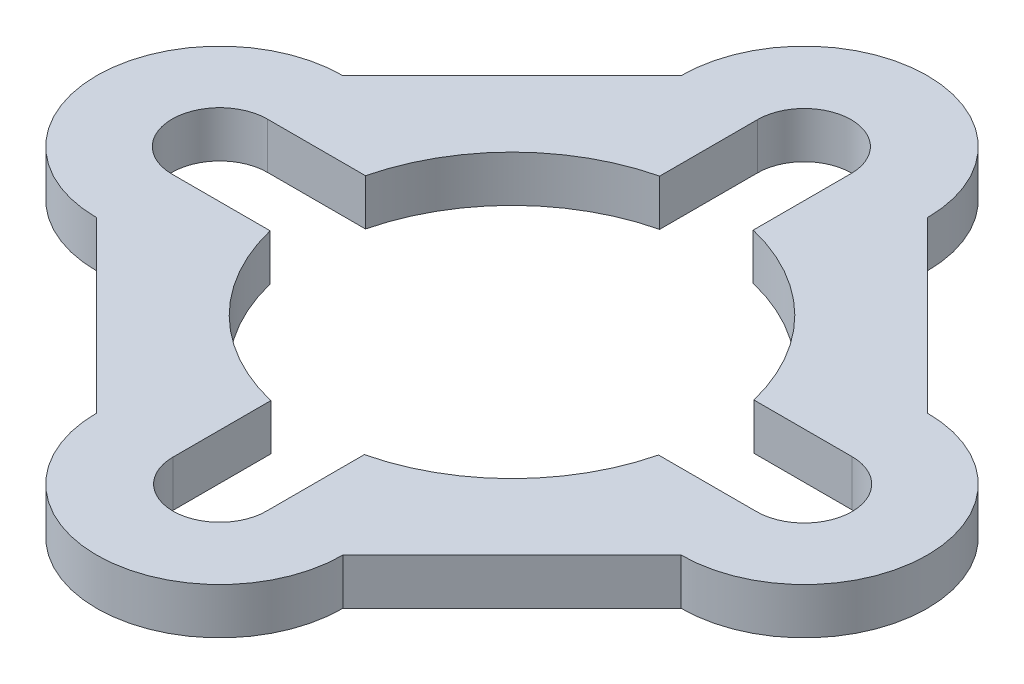
SolidWorks part; units mm, degrees
ref_plane "Front Plane" through (0, 0, 0) normal (0, 0, 1) x (1, 0, 0)
ref_plane "Top Plane" through (0, 0, 0) normal (0, 1, 0) x (1, 0, 0)
ref_plane "Right Plane" through (0, 0, 0) normal (1, 0, 0) x (0, 0, -1)
sketch "Sketch10" plane through (0, 0, 0) normal (0, 1, 0) x (1, 0, 0)
  line L0 (-9.5, 0) -> (9.5, 0) construction
  line L1 (-9.5, 1.55) -> (9.5, 1.55)
  line L2 (-9.5, -1.55) -> (9.5, -1.55)
  line L3 (0, 9.5) -> (0, -9.5) construction
  line L4 (1.52, 9.5) -> (1.52, -9.5)
  line L5 (-1.52, 9.5) -> (-1.52, -9.5)
  line L6 (-9.5, -4) -> (-4, -9.5)
  line L7 (4, -9.5) -> (9.5, -4)
  line L8 (9.5, 4) -> (4, 9.5)
  line L9 (-4, 9.5) -> (-9.5, 4)
  circle A4 centre (0, 0) radius 14.6 construction
  circle A5 centre (0, 0) radius 6.5
  arc A6 (-9.5, 1.55) -> (-9.5, -1.55) centre (-9.5, 0) ccw
  arc A7 (9.5, -1.55) -> (9.5, 1.55) centre (9.5, 0) ccw
  arc A8 (1.52, 9.5) -> (-1.52, 9.5) centre (0, 9.5) ccw
  arc A9 (-1.52, -9.5) -> (1.52, -9.5) centre (0, -9.5) ccw
  arc A11 (4, 9.5) -> (-4, 9.5) centre (0, 9.5) ccw
  arc A13 (-4, -9.5) -> (4, -9.5) centre (0, -9.5) ccw
  arc A14 (-9.5, 4) -> (-9.5, -4) centre (-9.5, 0) ccw
  arc A15 (9.5, -4) -> (9.5, 4) centre (9.5, 0) ccw
  point P1 (0, 0)
  point P4 (0, 0)
  point P9 (0, 0)
  point P14 (0, 0)
  dimension "D1" = 19
  dimension "D4" = 13
  dimension "D6" = 1.52
  dimension "D2" = 8
  dimension "D5" = 1.55
  dimension "D3" = 19
extrude "Boss-Extrude1" add sketch "Sketch10" along normal blind 1.5 contours L7 A15 L8 A11 L9 A14 L6 A13 A9 L5 A5 L2 A6 L1 A8 L4 A7
